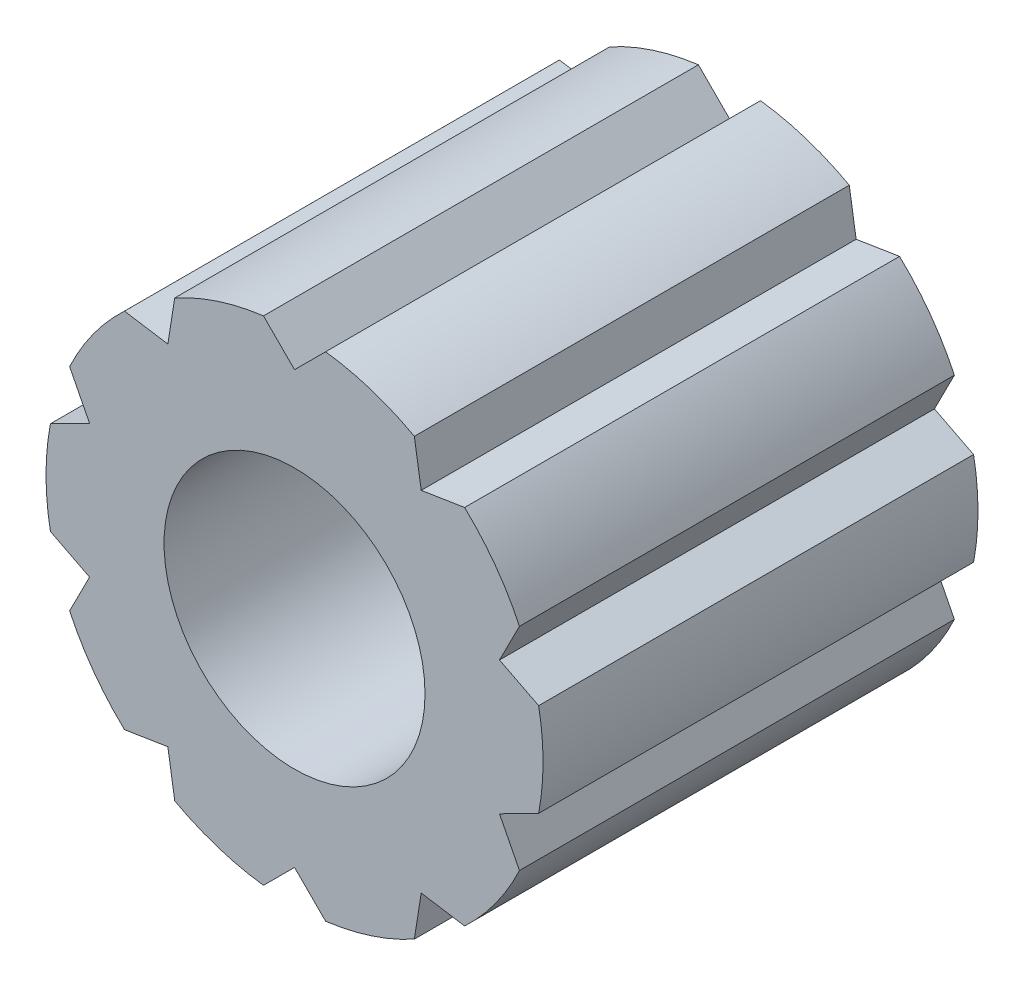
SolidWorks part; units mm, degrees
ref_plane "Front Plane" through (0, 0, 0) normal (0, 0, 1) x (1, 0, 0)
ref_plane "Top Plane" through (0, 0, 0) normal (0, 1, 0) x (1, 0, 0)
ref_plane "Right Plane" through (0, 0, 0) normal (1, 0, 0) x (0, 0, -1)
sketch "Sketch1" plane through (0, 0, 0) normal (0, 0, 1) x (1, 0, 0)
  line L1 (0.5, 3.9686) -> (0, 3.4686)
  line L2 (0, 3.4686) -> (-0.5, 3.9686)
  line L3 (2.7372, 2.9168) -> (2.0388, 2.8062)
  line L4 (2.0388, 2.8062) -> (1.9282, 3.5046)
  line L5 (3.9289, 0.7508) -> (3.2989, 1.0719)
  line L6 (3.2989, 1.0719) -> (3.6199, 1.7019)
  line L7 (3.6199, -1.7019) -> (3.2989, -1.0719)
  line L8 (3.2989, -1.0719) -> (3.9289, -0.7508)
  line L9 (1.9282, -3.5046) -> (2.0388, -2.8062)
  line L10 (2.0388, -2.8062) -> (2.7372, -2.9168)
  line L11 (-0.5, -3.9686) -> (0, -3.4686)
  line L12 (0, -3.4686) -> (0.5, -3.9686)
  line L13 (-2.7372, -2.9168) -> (-2.0388, -2.8062)
  line L14 (-2.0388, -2.8062) -> (-1.9282, -3.5046)
  line L15 (-3.9289, -0.7508) -> (-3.2989, -1.0719)
  line L16 (-3.2989, -1.0719) -> (-3.6199, -1.7019)
  line L17 (-3.6199, 1.7019) -> (-3.2989, 1.0719)
  line L18 (-3.2989, 1.0719) -> (-3.9289, 0.7508)
  line L19 (-1.9282, 3.5046) -> (-2.0388, 2.8062)
  line L20 (-2.0388, 2.8062) -> (-2.7372, 2.9168)
  circle A0 centre (0, 0) radius 2.1
  arc A1 (-0.5, 3.9686) -> (-1.9282, 3.5046) centre (0, 0) ccw
  arc A2 (1.9282, 3.5046) -> (0.5, 3.9686) centre (0, 0) ccw
  arc A3 (3.6199, 1.7019) -> (2.7372, 2.9168) centre (0, 0) ccw
  arc A4 (3.9289, -0.7508) -> (3.9289, 0.7508) centre (0, 0) ccw
  arc A5 (2.7372, -2.9168) -> (3.6199, -1.7019) centre (0, 0) ccw
  arc A6 (0.5, -3.9686) -> (1.9282, -3.5046) centre (0, 0) ccw
  arc A7 (-1.9282, -3.5046) -> (-0.5, -3.9686) centre (0, 0) ccw
  arc A8 (-3.6199, -1.7019) -> (-2.7372, -2.9168) centre (0, 0) ccw
  arc A9 (-3.9289, 0.7508) -> (-3.9289, -0.7508) centre (0, 0) ccw
  arc A10 (-2.7372, 2.9168) -> (-3.6199, 1.7019) centre (0, 0) ccw
  point P35 (0, 0)
  dimension "D1" = 4.2
  dimension "D2" = 8
  dimension "D3" = 0.5
  dimension "D4" = 1
  dimension "D5" = 10
extrude "Boss-Extrude1" add sketch "Sketch1" along normal blind 7
